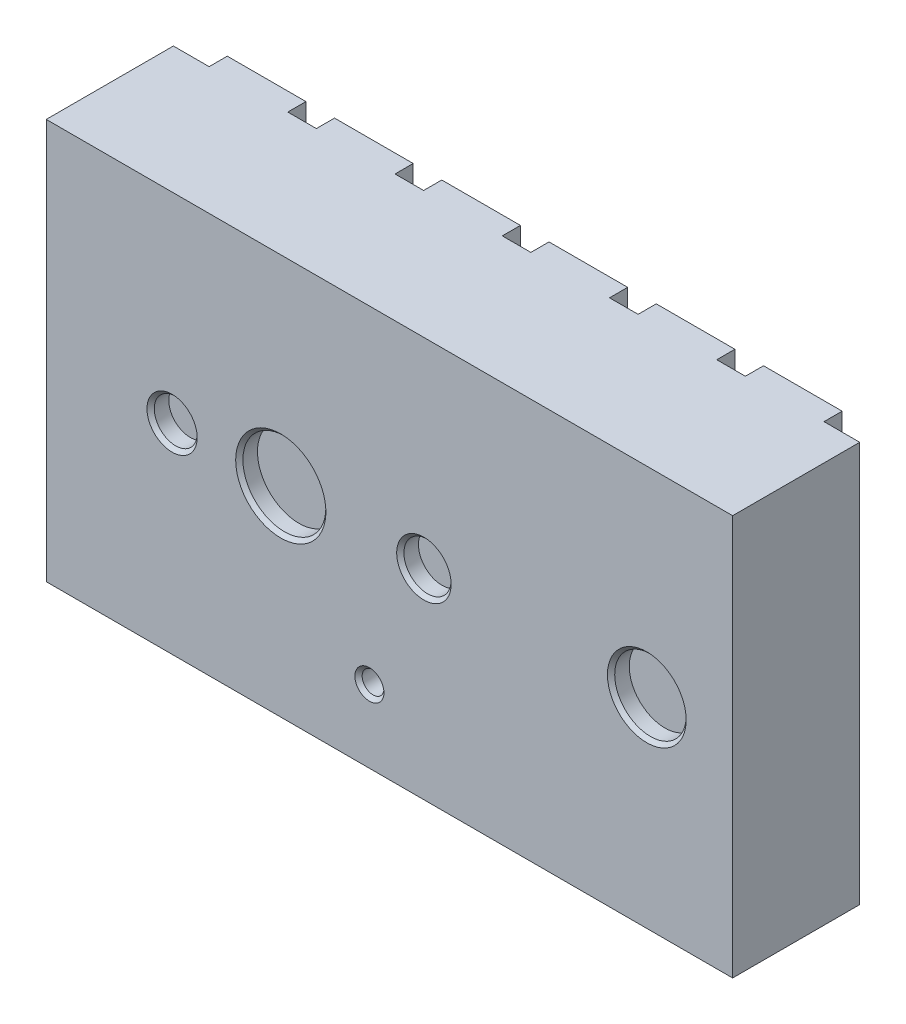
SolidWorks part; units mm, degrees
ref_plane "Front Plane" through (0, 0, 0) normal (0, 0, 1) x (1, 0, 0)
ref_plane "Top Plane" through (0, 0, 0) normal (0, 1, 0) x (1, 0, 0)
ref_plane "Right Plane" through (0, 0, 0) normal (1, 0, 0) x (0, 0, -1)
sketch "Sketch1" plane through (0, 0, 0) normal (0, 0, 1) x (1, 0, 0)
  line L1 (0, 0) -> (4.8, 0)
  line L2 (0, 0) -> (0, 2.8)
  line L3 (0, 2.8) -> (4.8, 2.8)
  line L4 (4.8, 0) -> (4.8, 2.8)
  dimension "D1" = 4.8
  dimension "D2" = 2.8
extrude "Boss-Extrude3" add sketch "Sketch1" along normal blind 0.889 contours L3 L4 L1 L2
sketch "Sketch5" plane through (0, 0, 0.889) normal (0, 0, 1) x (1, 0, 0)
  line L0 (0, 1.4) -> (4.8, 1.4) construction
  line L1 (0, 0) -> (0, 2.8) construction
  line L2 (4.8, 0) -> (4.8, 2.8) construction
  line L3 (0, 0) -> (4.8, 0) construction
  circle A0 centre (0.88, 1.4) radius 0.15
  circle A1 centre (1.64, 1.4) radius 0.29
  circle A2 centre (2.641, 1.4) radius 0.1651
  circle A3 centre (2.26, 0.508) radius 0.0762
  circle A4 centre (4.2, 1.4) radius 0.25
  dimension "D6" = 0.5
  dimension "D7" = 0.3302
  dimension "D8" = 0.58
  dimension "D9" = 0.3
  dimension "D11" = 0.1524
  dimension "D1" = 0.6
  dimension "D2" = 2.56
  dimension "D3" = 3.32
  dimension "D4" = 2.159
  dimension "D5" = 2.54
  dimension "D10" = 0.508
extrude "Cut-Extrude2" cut sketch "Sketch5" against normal blind 0.127
chamfer "Chamfer2" distance 0.0254 angle 45 5 edges at (2.3362, 0.508, 0.889) (1.03, 1.4, 0.889) (1.93, 1.4, 0.889) (2.8061, 1.4, 0.889) (4.45, 1.4, 0.889)
sketch "Sketch6" plane through (0, 0, 0) normal (0, 0, -1) x (-1, 0, 0)
  line L0 (0, 0) -> (-4.8, 0) construction
  line L1 (-0.25, 0) -> (-0.8, 0)
  line L2 (-0.25, 0) -> (-0.25, 0.7)
  line L3 (-0.25, 0.7) -> (-0.8, 0.7)
  line L4 (-0.8, 0) -> (-0.8, 0.7)
  line L5 (0, 0) -> (0, 2.8) construction
  dimension "D1" = 0.25
  dimension "D2" = 0.55
  dimension "D3" = 0.7
extrude "Boss-Extrude4" add sketch "Sketch6" along normal blind 0.127 separate body
pattern_linear "LPattern1" count 6 spacing 0.75 along (1, 0, 0) count 2 spacing 2.1 along (0, 1, 0) of "Boss-Extrude4"
